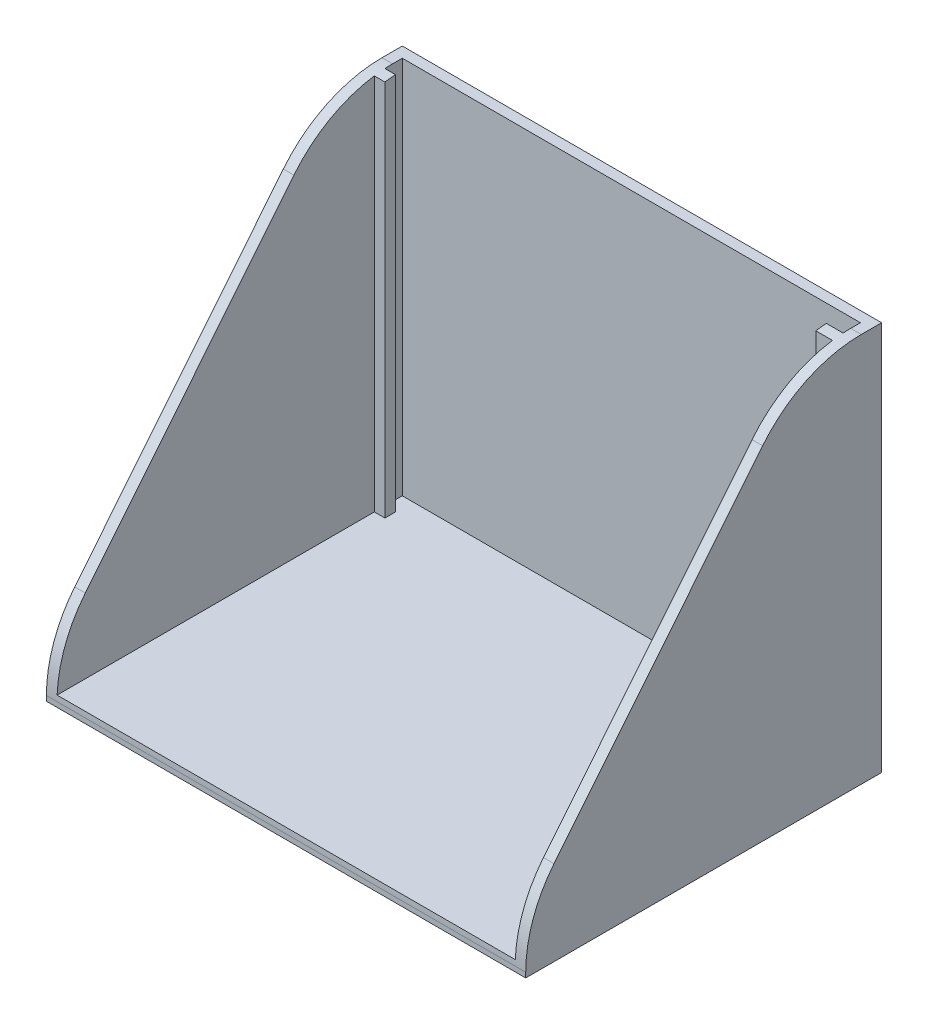
SolidWorks part; units mm, degrees
ref_plane "Front Plane" through (0, 0, 0) normal (0, 0, 1) x (1, 0, 0)
ref_plane "Top Plane" through (0, 0, 0) normal (0, 1, 0) x (1, 0, 0)
ref_plane "Right Plane" through (0, 0, 0) normal (1, 0, 0) x (0, 0, -1)
sketch "Sketch1" plane through (0, -154.6818, 0) normal (0, -1, 0) x (1, 0, 0)
  line L1 (108.516, 1.834) -> (107.246, 1.834)
  line L2 (107.246, 1.834) -> (107.246, -0.254)
  line L3 (107.246, -0.254) -> (146.4426, -0.254)
  line L5 (163.524, -1.524) -> (105.976, -1.524)
  line L6 (105.976, -1.524) -> (105.976, 3.104)
  line L7 (105.976, 3.104) -> (108.516, 3.104)
  line L8 (108.516, 3.104) -> (108.516, 1.834)
  line L9 (162, 1.58) -> (107.5, 1.58) construction
  line L10 (162, 0) -> (107.5, 0) construction
  line L11 (107.5, 0) -> (107.5, 1.58) construction
  line L12 (163.524, -1.524) -> (163.524, 3.104)
  line L13 (107.5, 1.58) -> (162, 1.58) construction
  line L14 (107.5, 1.58) -> (107.5, 0) construction
  line L15 (107.5, 0) -> (162, 0) construction
  line L16 (162, 1.58) -> (162, 0) construction
  line L19 (162, 1.58) -> (162, 0) construction
  line L20 (163.524, 3.104) -> (160.2529, 3.104)
  line L21 (160.2529, 3.104) -> (160.2529, 1.834)
  line L22 (160.2529, 1.834) -> (162.254, 1.834)
  line L23 (162.254, 1.834) -> (162.254, -0.254)
  line L24 (162.254, -0.254) -> (146.4426, -0.254)
  dimension "D1" = 0.254
  dimension "D2" = 0.254
  dimension "D3" = 0.254
  dimension "D4" = 1.27
  dimension "D6" = 1.27
  dimension "D8" = 1.27
  dimension "D5" = 0.254
  dimension "D7" = 0.254
  dimension "D9" = 1.27
  dimension "D10" = 1.27
  dimension "D11" = 1.27
extrude "Boss-Extrude1" add sketch "Sketch1" against normal up to vertex (45.5 mm away)
sketch "Sketch2" plane through (0, -154.6818, 0) normal (0, -1, 0) x (1, 0, 0)
  line L0 (163.524, -1.524) -> (163.524, 3.104) construction
  line L1 (105.976, 3.104) -> (163.524, 3.104)
  line L2 (105.976, 3.104) -> (105.976, -1.524)
  line L3 (105.976, -1.524) -> (163.524, -1.524)
  line L4 (163.524, 3.104) -> (163.524, -1.524)
  line L5 (105.976, -1.524) -> (163.524, -1.524) construction
  point P6 (163.524, -1.524)
extrude "Boss-Extrude2" add sketch "Sketch2" along normal blind 1.27
sketch "Sketch8" plane through (0, 0, 3.104) normal (0, 0, 1) x (1, 0, 0)
  line L0 (105.976, -109.1818) -> (107.246, -109.1818)
  line L1 (162.254, -109.1818) -> (107.246, -109.1818) construction
  line L2 (107.246, -109.1818) -> (107.246, -154.6818)
  line L3 (107.246, -154.6818) -> (162.254, -154.6818)
  line L4 (162.254, -154.6818) -> (162.254, -109.1818)
  line L5 (163.524, -109.1818) -> (160.2529, -109.1818) construction
  line L6 (162.254, -109.1818) -> (163.524, -109.1818)
  line L7 (163.524, -109.1818) -> (163.524, -155.9518)
  line L8 (163.524, -155.9518) -> (105.976, -155.9518)
  line L9 (105.976, -155.9518) -> (105.976, -109.1818)
  dimension "D1" = 1.27
  dimension "D2" = 1.27
  dimension "D3" = 1.27
extrude "Boss-Extrude3" add sketch "Sketch8" along normal blind 38.1
chamfer "Chamfer2" distance 33.02 angle 51 2 edges at (162.889, -109.1818, 41.204) (106.611, -109.1818, 41.204)
fillet "Fillet2" radius 15.24 2 edges at (162.889, -109.1818, 8.184) (106.611, -109.1818, 8.184)
fillet "Fillet3" radius 15.24 1 edges at (106.611, -149.9581, 41.204)
sketch "Sketch9" plane through (0, 0, -1.524) normal (0, 0, -1) x (-1, 0, 0)
equation "\"D1@Sketch1\"=\"tolerance@Clock1.Assembly\""
equation "\"D2@Sketch1\"=\"tolerance@Clock1.Assembly\""
equation "\"D3@Sketch1\"=\"tolerance@Clock1.Assembly\""
equation "\"D4@Sketch1\"=\"wall_thickness@Clock1.Assembly\""
equation "\"D6@Sketch1\"=\"wall_thickness@Clock1.Assembly\""
equation "\"D8@Sketch1\"=\"wall_thickness@Clock1.Assembly\""
equation "\"D1@Boss-Extrude2\"=\"wall_thickness@Clock1.Assembly\""
equation "\"D5@Sketch1\"=\"tolerance@Clock1.Assembly\""
equation "\"D7@Sketch1\"=\"tolerance@Clock1.Assembly\""
equation "\"D9@Sketch1\"=\"wall_thickness@Clock1.Assembly\""
equation "\"D10@Sketch1\"=\"wall_thickness@Clock1.Assembly\""
equation "\"D11@Sketch1\"=\"wall_thickness@Clock1.Assembly\""
equation "\"D1@Sketch8\"=\"wall_thickness@Clock1.Assembly\""
equation "\"D2@Sketch8\"=\"wall_thickness@Clock1.Assembly\""
equation "\"D3@Sketch8\"=\"wall_thickness@Clock1.Assembly\""
